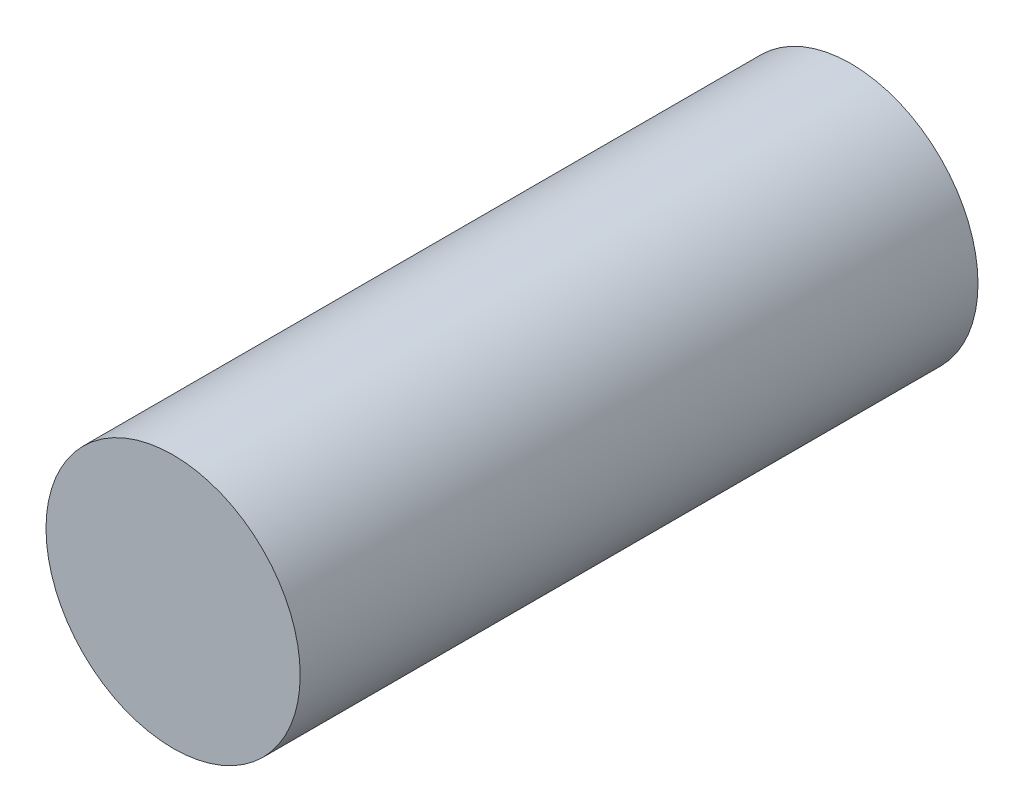
SolidWorks part; units mm, degrees
material "Alloy Steel"
ref_plane "Front Plane" through (0, 0, 0) normal (0, 0, 1) x (1, 0, 0)
ref_plane "Top Plane" through (0, 0, 0) normal (0, 1, 0) x (1, 0, 0)
ref_plane "Right Plane" through (0, 0, 0) normal (1, 0, 0) x (0, 0, -1)
sketch "Sketch1" plane through (0, 0, 0) normal (0, 0, 1) x (1, 0, 0)
  circle A0 centre (0, 0) radius 4.7625
  dimension "D1" = 9.525
extrude "Boss-Extrude1" add sketch "Sketch1" along normal blind 25.4
